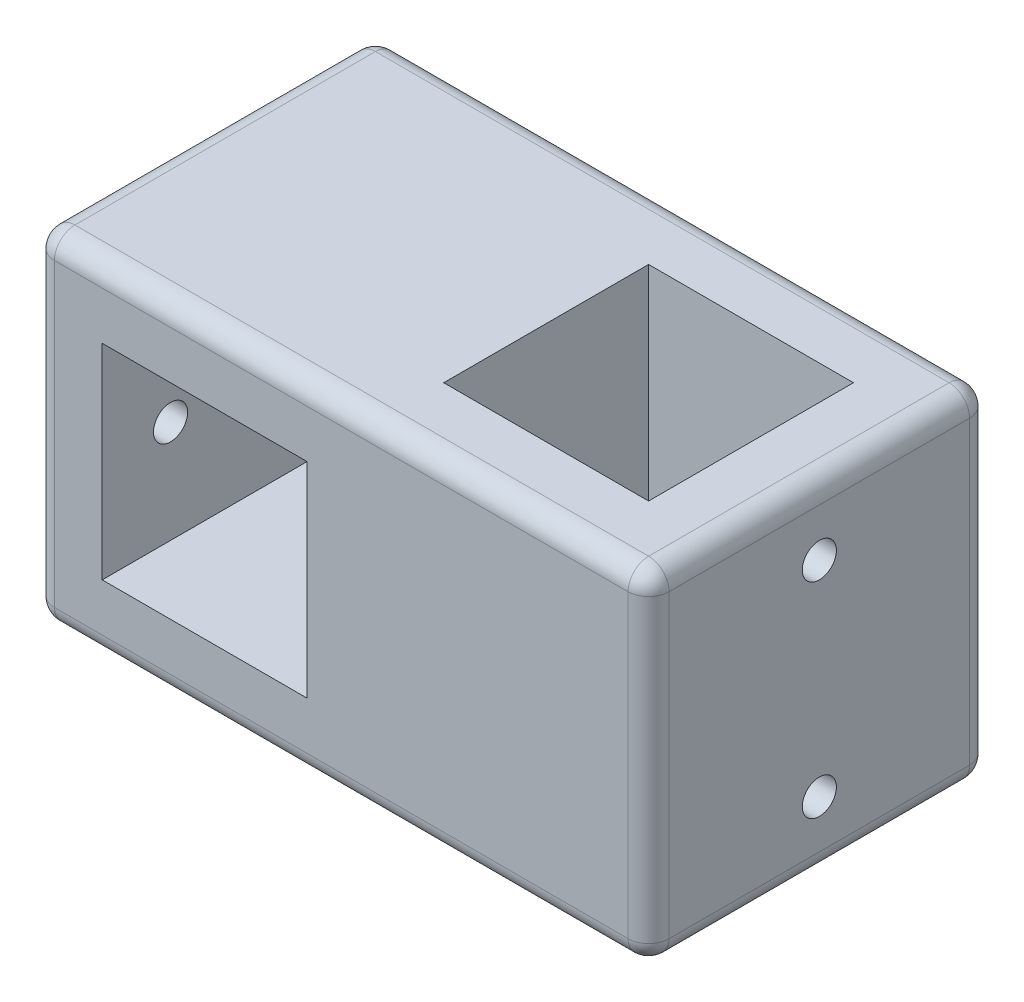
SolidWorks part; units mm, degrees
ref_plane "Front Plane" through (0, 0, 0) normal (0, 0, 1) x (1, 0, 0)
ref_plane "Top Plane" through (0, 0, 0) normal (0, 1, 0) x (1, 0, 0)
ref_plane "Right Plane" through (0, 0, 0) normal (1, 0, 0) x (0, 0, -1)
sketch "Sketch1" plane through (0, 0, 0) normal (0, 0, 1) x (1, 0, 0)
  line L1 (45, -25) -> (-45, -25)
  line L2 (45, -25) -> (45, 25)
  line L3 (45, 25) -> (-45, 25)
  line L4 (-45, -25) -> (-45, 25)
  line L5 (45, -25) -> (-45, 25) construction
  line L6 (45, 25) -> (-45, -25) construction
  point P0 (0, 0)
  dimension "D1" = 90
  dimension "D2" = 50
extrude "Boss-Extrude1" add sketch "Sketch1" along normal blind 50
sketch "Sketch2" plane through (0, 0, 50) normal (0, 0, 1) x (1, 0, 0)
  line L0 (-45, 0) -> (45, 0) construction
  line L1 (-45, 25) -> (-45, -25) construction
  line L2 (45, -25) -> (45, 25) construction
  line L4 (-5, -15) -> (-35, -15)
  line L5 (-5, -15) -> (-5, 15)
  line L6 (-5, 15) -> (-35, 15)
  line L7 (-35, -15) -> (-35, 15)
  line L8 (-5, -15) -> (-35, 15) construction
  line L9 (-5, 15) -> (-35, -15) construction
  point P6 (-20, 0)
  dimension "D1" = 30
  dimension "D2" = 30
  dimension "D3" = 10
extrude "Cut-Extrude1" cut sketch "Sketch2" against normal up to next
sketch "Sketch3" plane through (0, 25, 0) normal (0, 1, 0) x (1, 0, 0)
  line L0 (-45, -25) -> (45, -25) construction
  line L1 (-45, -50) -> (-45, 0) construction
  line L2 (45, -50) -> (45, 0) construction
  line L4 (35, -10) -> (5, -10)
  line L5 (35, -10) -> (35, -40)
  line L6 (35, -40) -> (5, -40)
  line L7 (5, -10) -> (5, -40)
  line L8 (35, -10) -> (5, -40) construction
  line L9 (35, -40) -> (5, -10) construction
  point P6 (20, -25)
  dimension "D1" = 30
  dimension "D2" = 30
  dimension "D3" = 10
extrude "Cut-Extrude2" cut sketch "Sketch3" against normal up to next
fillet "Fillet1" radius 3 12 edges at (-45, 25, 25) (-45, -25, 25) (0, -25, 0) (0, -25, 50) (45, -25, 25) (45, 25, 25) (0, 25, 50) (0, 25, 0) (-45, 0, 50) (-45, 0, 0) (45, 0, 0) (45, 0, 50)
sketch "Sketch4" plane through (-45, 0, 0) normal (-1, 0, 0) x (0, 0, 1)
  line L0 (0, 0) -> (50, 0) construction
  line L1 (50, 22) -> (50, -22) construction
  line L2 (0, -22) -> (0, 22) construction
  circle A0 centre (10, 0) radius 2.5
  circle A1 centre (40, 0) radius 2.5
  dimension "D3" = 5
  dimension "D4" = 5
  dimension "D1" = 10
  dimension "D2" = 10
extrude "Cut-Extrude3" cut sketch "Sketch4" against normal up to next
sketch "Sketch5" plane through (45, 0, 0) normal (1, 0, 0) x (0, 0, -1)
  line L0 (-25, -25) -> (-25, 25) construction
  line L1 (-3, -25) -> (-47, -25) construction
  line L2 (-47, 25) -> (-3, 25) construction
  circle A0 centre (-25, 15) radius 2.5
  circle A1 centre (-25, -15) radius 2.5
  dimension "D3" = 5
  dimension "D4" = 5
  dimension "D1" = 10
  dimension "D2" = 10
extrude "Cut-Extrude4" cut sketch "Sketch5" against normal up to next
